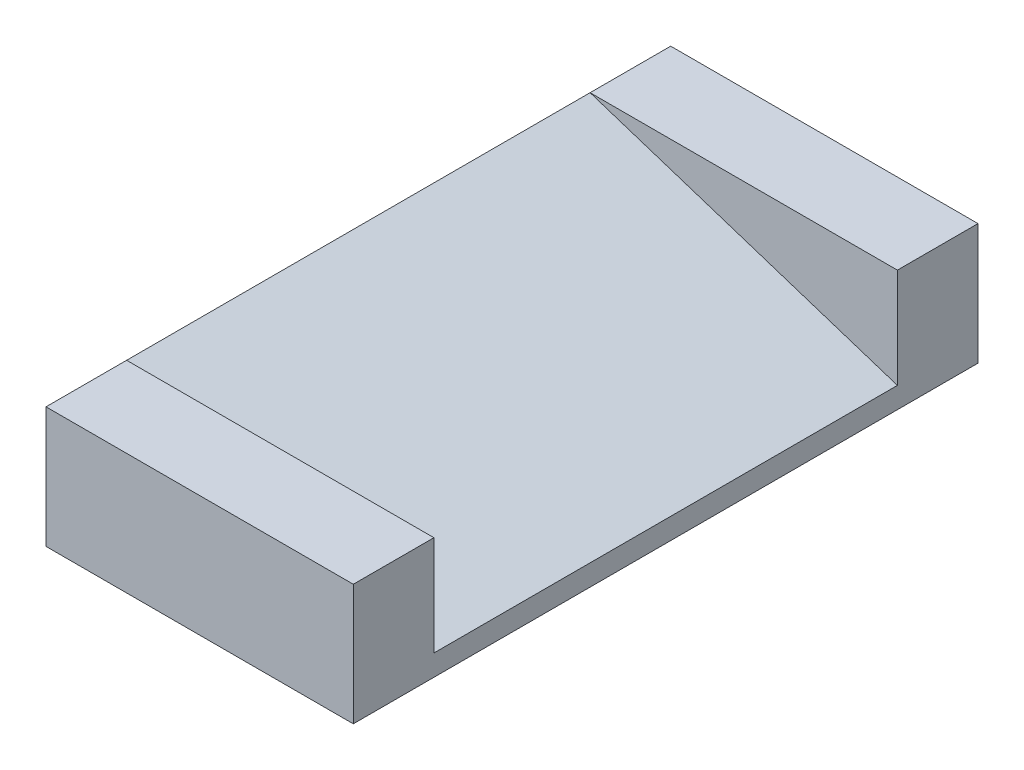
SolidWorks part; units mm, degrees
ref_plane "Front Plane" through (0, 0, 0) normal (0, 0, 1) x (1, 0, 0)
ref_plane "Top Plane" through (0, 0, 0) normal (0, 1, 0) x (1, 0, 0)
ref_plane "Right Plane" through (0, 0, 0) normal (1, 0, 0) x (0, 0, -1)
sketch "Sketch1" plane through (0, 0, 0) normal (0, 1, 0) x (1, 0, 0)
  line L8 (-55.8145, 0) -> (89.5807, 0) construction
  line L9 (-15.25, 31) -> (15.25, 31)
  line L10 (-15.25, 31) -> (-15.25, -31)
  line L11 (-15.25, -31) -> (15.25, -31)
  line L12 (15.25, 31) -> (15.25, -31)
  line L13 (0, 63.6778) -> (0, -76.9376) construction
  dimension "D1" = 62
  dimension "D2" = 30.5
extrude "Boss-Extrude1" add sketch "Sketch1" along normal blind 12
ref_plane "Plane1" through (0, 0, -23) normal (0, 0, -1) x (-1, 0, 0)
ref_plane "Plane2" through (0, 0, 23) normal (0, 0, 1) x (1, 0, 0)
sketch "Sketch2" plane through (0, 0, -23) normal (0, 0, -1) x (-1, 0, 0)
  line L0 (-15.25, 12) -> (15.25, 12)
  line L1 (15.25, 12) -> (-15.25, 2.0899)
  line L2 (-15.25, 12) -> (-15.25, 0) construction
  line L3 (-15.25, 2.0899) -> (-15.25, 12)
  dimension "D1" = 18
extrude "Cut-Extrude1" cut sketch "Sketch2" against normal up to surface (46 mm away)
